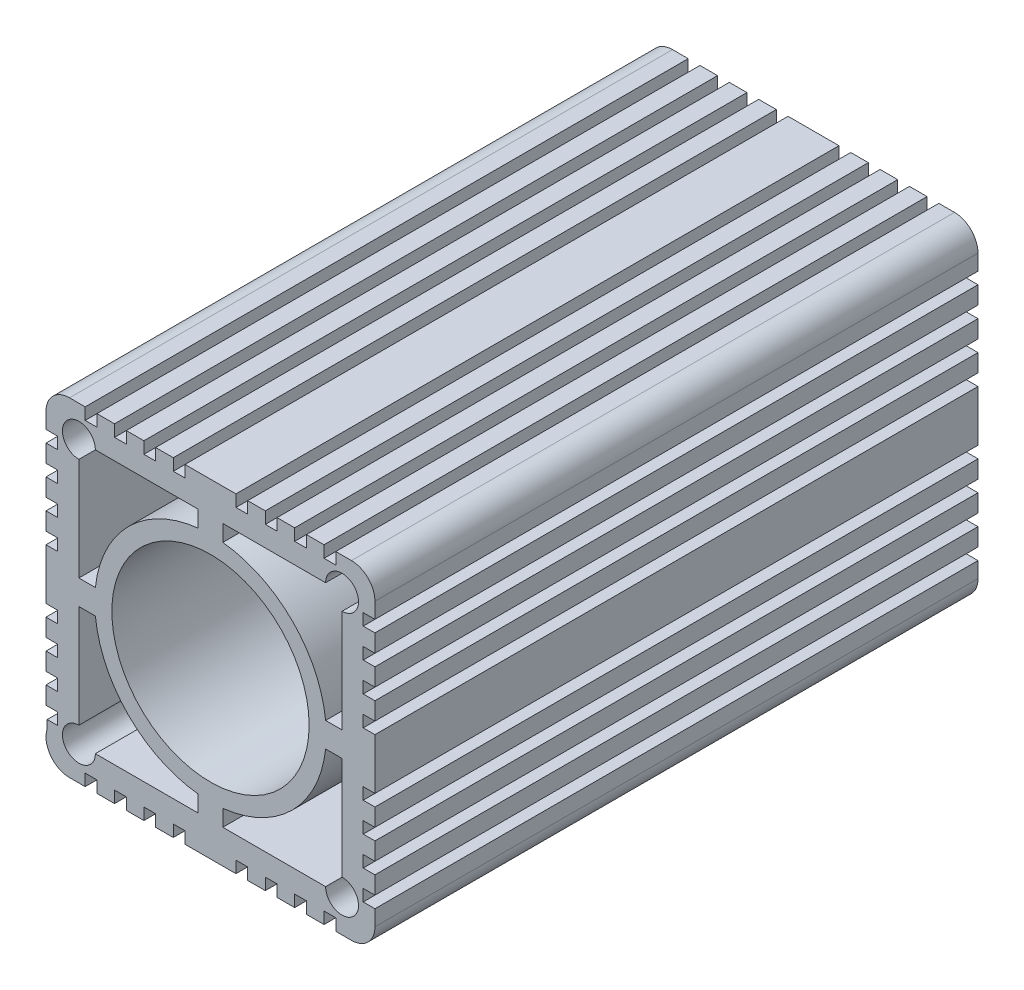
SolidWorks part; units mm, degrees
ref_plane "Front Plane" through (0, 0, 0) normal (0, 0, 1) x (1, 0, 0)
ref_plane "Top Plane" through (0, 0, 0) normal (0, 1, 0) x (1, 0, 0)
ref_plane "Right Plane" through (0, 0, 0) normal (1, 0, 0) x (0, 0, -1)
sketch "Sketch3" plane through (0, 0, 0) normal (0, 0, 1) x (-1, 0, 0)
  line L0 (-12, 10.5) -> (-12, 1.125)
  line L1 (-1.125, 12) -> (-10.5, 12)
  line L2 (-1.125, 10.5) -> (-1.125, 12)
  line L3 (-12, 1.125) -> (-10.5, 1.125)
  line L4 (12, -10.5) -> (12, -1.125)
  line L5 (1.125, -12) -> (10.5, -12)
  line L6 (1.125, -10.5) -> (1.125, -12)
  line L7 (12, -1.125) -> (10.5, -1.125)
  line L8 (-10.5, -12) -> (-1.125, -12)
  line L9 (-12, -1.125) -> (-12, -10.5)
  line L10 (-10.5, -1.125) -> (-12, -1.125)
  line L11 (-1.125, -12) -> (-1.125, -10.5)
  line L12 (10.5, 12) -> (1.125, 12)
  line L13 (12, 1.125) -> (12, 10.5)
  line L14 (10.5, 1.125) -> (12, 1.125)
  line L15 (1.125, 12) -> (1.125, 10.5)
  line L16 (-14.9988, -10.2885) -> (-13.9274, -10.2885)
  line L17 (-13.9274, -10.2885) -> (-13.9274, -11.3599)
  line L18 (-13.9274, -11.3599) -> (-14.9988, -11.3599)
  line L19 (-14.9988, -11.3599) -> (-14.9988, -12.7885)
  line L20 (-12.856, -14.9313) -> (-11.4274, -14.9313)
  line L21 (-11.4274, -14.9313) -> (-11.4274, -13.8599)
  line L22 (-11.4274, -13.8599) -> (-10.356, -13.8599)
  line L23 (-10.356, -13.8599) -> (-10.356, -14.9313)
  line L24 (-10.356, -14.9313) -> (-8.7488, -14.9313)
  line L25 (-8.7488, -14.9313) -> (-8.7488, -13.8599)
  line L26 (-8.7488, -13.8599) -> (-7.6774, -13.8599)
  line L27 (-7.6774, -13.8599) -> (-7.6774, -14.9313)
  line L28 (-7.6774, -14.9313) -> (-6.0702, -14.9313)
  line L29 (-6.0702, -14.9313) -> (-6.0702, -13.8599)
  line L30 (-6.0702, -13.8599) -> (-4.9988, -13.8599)
  line L31 (-4.9988, -13.8599) -> (-4.9988, -14.9313)
  line L32 (-4.9988, -14.9313) -> (-3.3917, -14.9313)
  line L33 (-3.3917, -14.9313) -> (-3.3917, -13.8599)
  line L34 (-3.3917, -13.8599) -> (-2.3202, -13.8599)
  line L35 (-2.3202, -13.8599) -> (-2.3202, -14.9313)
  line L36 (-2.3202, -14.9313) -> (2.3226, -14.9313)
  line L37 (2.3226, -14.9313) -> (2.3226, -13.8599)
  line L38 (2.3226, -13.8599) -> (3.394, -13.8599)
  line L39 (3.394, -13.8599) -> (3.394, -14.9313)
  line L40 (3.394, -14.9313) -> (5.0012, -14.9313)
  line L41 (5.0012, -14.9313) -> (5.0012, -13.8599)
  line L42 (5.0012, -13.8599) -> (6.0726, -13.8599)
  line L43 (6.0726, -13.8599) -> (6.0726, -14.9313)
  line L44 (6.0726, -14.9313) -> (7.6798, -14.9313)
  line L45 (7.6798, -14.9313) -> (7.6798, -13.8599)
  line L46 (7.6798, -13.8599) -> (8.7512, -13.8599)
  line L47 (8.7512, -13.8599) -> (8.7512, -14.9313)
  line L48 (8.7512, -14.9313) -> (10.3583, -14.9313)
  line L49 (10.3583, -14.9313) -> (10.3583, -13.8599)
  line L50 (10.3583, -13.8599) -> (11.4298, -13.8599)
  line L51 (11.4298, -13.8599) -> (11.4298, -14.9313)
  line L52 (11.4298, -14.9313) -> (12.8583, -14.9313)
  line L53 (15.0012, -12.7885) -> (15.0012, -11.3599)
  line L54 (15.0012, -11.3599) -> (13.9298, -11.3599)
  line L55 (13.9298, -11.3599) -> (13.9298, -10.2885)
  line L56 (13.9298, -10.2885) -> (15.0012, -10.2885)
  line L57 (15.0012, -10.2885) -> (15.0012, -8.6813)
  line L58 (15.0012, -8.6813) -> (13.9298, -8.6813)
  line L59 (13.9298, -8.6813) -> (13.9298, -7.6099)
  line L60 (13.9298, -7.6099) -> (15.0012, -7.6099)
  line L61 (15.0012, -7.6099) -> (15.0012, -6.0027)
  line L62 (15.0012, -6.0027) -> (13.9298, -6.0027)
  line L63 (13.9298, -6.0027) -> (13.9298, -4.9313)
  line L64 (13.9298, -4.9313) -> (15.0012, -4.9313)
  line L65 (15.0012, -4.9313) -> (15.0012, -3.3242)
  line L66 (15.0012, -3.3242) -> (13.9298, -3.3242)
  line L67 (13.9298, -3.3242) -> (13.9298, -2.2527)
  line L68 (13.9298, -2.2527) -> (15.0012, -2.2527)
  line L69 (15.0012, -2.2527) -> (15.0012, 2.3901)
  line L70 (15.0012, 2.3901) -> (13.9298, 2.3901)
  line L71 (13.9298, 2.3901) -> (13.9298, 3.4615)
  line L72 (13.9298, 3.4615) -> (15.0012, 3.4615)
  line L73 (15.0012, 3.4615) -> (15.0012, 5.0687)
  line L74 (15.0012, 5.0687) -> (13.9298, 5.0687)
  line L75 (13.9298, 5.0687) -> (13.9298, 6.1401)
  line L76 (13.9298, 6.1401) -> (15.0012, 6.1401)
  line L77 (15.0012, 6.1401) -> (15.0012, 7.7473)
  line L78 (15.0012, 7.7473) -> (13.9298, 7.7473)
  line L79 (13.9298, 7.7473) -> (13.9298, 8.8187)
  line L80 (13.9298, 8.8187) -> (15.0012, 8.8187)
  line L81 (15.0012, 8.8187) -> (15.0012, 10.4258)
  line L82 (15.0012, 10.4258) -> (13.9298, 10.4258)
  line L83 (13.9298, 10.4258) -> (13.9298, 11.4973)
  line L84 (13.9298, 11.4973) -> (14.894, 11.4973)
  line L85 (14.894, 11.4973) -> (14.894, 12.2567)
  line L86 (12.8583, 15.0687) -> (11.4298, 15.0687)
  line L87 (11.4298, 15.0687) -> (11.4298, 13.9973)
  line L88 (11.4298, 13.9973) -> (10.3583, 13.9973)
  line L89 (10.3583, 13.9973) -> (10.3583, 15.0687)
  line L90 (10.3583, 15.0687) -> (8.7512, 15.0687)
  line L91 (8.7512, 15.0687) -> (8.7512, 13.9973)
  line L92 (8.7512, 13.9973) -> (7.6798, 13.9973)
  line L93 (7.6798, 13.9973) -> (7.6798, 15.0687)
  line L94 (7.6798, 15.0687) -> (6.0726, 15.0687)
  line L95 (6.0726, 15.0687) -> (6.0726, 13.9973)
  line L96 (6.0726, 13.9973) -> (5.0012, 13.9973)
  line L97 (5.0012, 13.9973) -> (5.0012, 15.0687)
  line L98 (5.0012, 15.0687) -> (3.394, 15.0687)
  line L99 (3.394, 15.0687) -> (3.394, 13.9973)
  line L100 (3.394, 13.9973) -> (2.3226, 13.9973)
  line L101 (2.3226, 13.9973) -> (2.3226, 15.0687)
  line L102 (2.3226, 15.0687) -> (-2.3202, 15.0687)
  line L103 (-2.3202, 15.0687) -> (-2.3202, 13.9973)
  line L104 (-2.3202, 13.9973) -> (-3.3917, 13.9973)
  line L105 (-3.3917, 13.9973) -> (-3.3917, 15.0687)
  line L106 (-3.3917, 15.0687) -> (-4.9988, 15.0687)
  line L107 (-4.9988, 15.0687) -> (-4.9988, 13.9973)
  line L108 (-4.9988, 13.9973) -> (-6.0702, 13.9973)
  line L109 (-6.0702, 13.9973) -> (-6.0702, 15.0687)
  line L110 (-6.0702, 15.0687) -> (-7.6774, 15.0687)
  line L111 (-7.6774, 15.0687) -> (-7.6774, 13.9973)
  line L112 (-7.6774, 13.9973) -> (-8.7488, 13.9973)
  line L113 (-8.7488, 13.9973) -> (-8.7488, 15.0687)
  line L114 (-8.7488, 15.0687) -> (-10.356, 15.0687)
  line L115 (-10.356, 15.0687) -> (-10.356, 13.9973)
  line L116 (-10.356, 13.9973) -> (-11.4274, 13.9973)
  line L117 (-11.4274, 13.9973) -> (-11.4274, 15.0687)
  line L118 (-11.4274, 15.0687) -> (-12.856, 15.0687)
  line L119 (-14.9988, 12.9258) -> (-14.9988, 11.4973)
  line L120 (-14.9988, 11.4973) -> (-13.9274, 11.4973)
  line L121 (-13.9274, 11.4973) -> (-13.9274, 10.4258)
  line L122 (-13.9274, 10.4258) -> (-14.9988, 10.4258)
  line L123 (-14.9988, 10.4258) -> (-14.9988, 8.8187)
  line L124 (-14.9988, 8.8187) -> (-13.9274, 8.8187)
  line L125 (-13.9274, 8.8187) -> (-13.9274, 7.7473)
  line L126 (-13.9274, 7.7473) -> (-14.9988, 7.7473)
  line L127 (-14.9988, 7.7473) -> (-14.9988, 6.1401)
  line L128 (-14.9988, 6.1401) -> (-13.9274, 6.1401)
  line L129 (-13.9274, 6.1401) -> (-13.9274, 5.0687)
  line L130 (-13.9274, 5.0687) -> (-14.9988, 5.0687)
  line L131 (-14.9988, 5.0687) -> (-14.9988, 3.4615)
  line L132 (-14.9988, 3.4615) -> (-13.9274, 3.4615)
  line L133 (-13.9274, 3.4615) -> (-13.9274, 2.3901)
  line L134 (-13.9274, 2.3901) -> (-14.9988, 2.3901)
  line L135 (-14.9988, 2.3901) -> (-14.9988, -2.2527)
  line L136 (-14.9988, -2.2527) -> (-13.9274, -2.2527)
  line L137 (-13.9274, -2.2527) -> (-13.9274, -3.3242)
  line L138 (-13.9274, -3.3242) -> (-14.9988, -3.3242)
  line L139 (-14.9988, -3.3242) -> (-14.9988, -4.9313)
  line L140 (-14.9988, -4.9313) -> (-13.9274, -4.9313)
  line L141 (-13.9274, -4.9313) -> (-13.9274, -6.0027)
  line L142 (-13.9274, -6.0027) -> (-14.9988, -6.0027)
  line L143 (-14.9988, -6.0027) -> (-14.9988, -7.6099)
  line L144 (-14.9988, -7.6099) -> (-13.9274, -7.6099)
  line L145 (-13.9274, -7.6099) -> (-13.9274, -8.6813)
  line L146 (-13.9274, -8.6813) -> (-14.9988, -8.6813)
  line L147 (-14.9988, -8.6813) -> (-14.9988, -10.2885)
  arc A0 (-10.5, 12) -> (-12, 10.5) centre (-12, 12) ccw
  arc A1 (-1.125, 10.5) -> (-10.5, 1.125) centre (0, 0) ccw
  arc A2 (10.5, -12) -> (12, -10.5) centre (12, -12) ccw
  arc A3 (1.125, -10.5) -> (10.5, -1.125) centre (0, 0) ccw
  arc A4 (-12, -10.5) -> (-10.5, -12) centre (-12, -12) ccw
  arc A5 (-10.5, -1.125) -> (-1.125, -10.5) centre (0, 0) ccw
  arc A6 (12, 10.5) -> (10.5, 12) centre (12, 12) ccw
  arc A7 (10.5, 1.125) -> (1.125, 10.5) centre (0, 0) ccw
  arc A8 (-14.9988, -12.7885) -> (-12.856, -14.9313) centre (-12.856, -12.7885) ccw
  arc A9 (12.8583, -14.9313) -> (15.0012, -12.7885) centre (12.8583, -12.7885) ccw
  arc A10 (14.894, 12.2567) -> (12.8583, 15.0687) centre (12.8583, 12.9258) ccw
  arc A11 (-12.856, 15.0687) -> (-14.9988, 12.9258) centre (-12.856, 12.9258) ccw
  circle A12 centre (0, 0) radius 8.9965
  dimension "D1" = 30
extrude "Boss-Extrude1" add sketch "Sketch3" along normal blind 55
sketch "Sketch4" plane through (0, -15.0687, 0) normal (0, -1, 0) x (1, 0, 0)
  line L1 (-12.8754, 17.4556) -> (12.8501, 17.4556)
  line L2 (-12.8754, 17.4556) -> (-12.8754, 2.4556)
  line L3 (-12.8754, 2.4556) -> (12.8501, 2.4556)
  line L4 (12.8501, 17.4556) -> (12.8501, 2.4556)
  line L5 (-12.8754, 17.4556) -> (12.8501, 2.4556) construction
  line L6 (-12.8754, 2.4556) -> (12.8501, 17.4556) construction
  point P0 (-0.0127, 9.9556)
  dimension "D1" = 15
extrude "Boss-Extrude2" add sketch "Sketch4" against normal blind 3
sketch "Sketch5" plane through (0, -15.0687, 0) normal (0, -1, 0) x (1, 0, 0)
  line L0 (-0.0012, 55) -> (-0.0012, 0) construction
  line L1 (-2.3226, 55) -> (2.3202, 55) construction
  line L2 (-2.3226, 0) -> (2.3202, 0) construction
  line L3 (-7.6798, 17.4556) -> (-8.7512, 17.4556) construction
  line L4 (7.6774, 17.4556) -> (8.7488, 17.4556) construction
  circle A0 centre (9.9188, 12.4556) radius 1.5
  circle A1 centre (-9.9212, 12.4556) radius 1.5
  point P10 (-8.2155, 17.4556)
  point P13 (8.2131, 17.4556)
  dimension "D1" = 9.92
  dimension "D2" = 9.92
  dimension "D4" = 5
  dimension "D3" = 5
extrude "Cut-Extrude1" cut sketch "Sketch5" against normal blind 3.5
